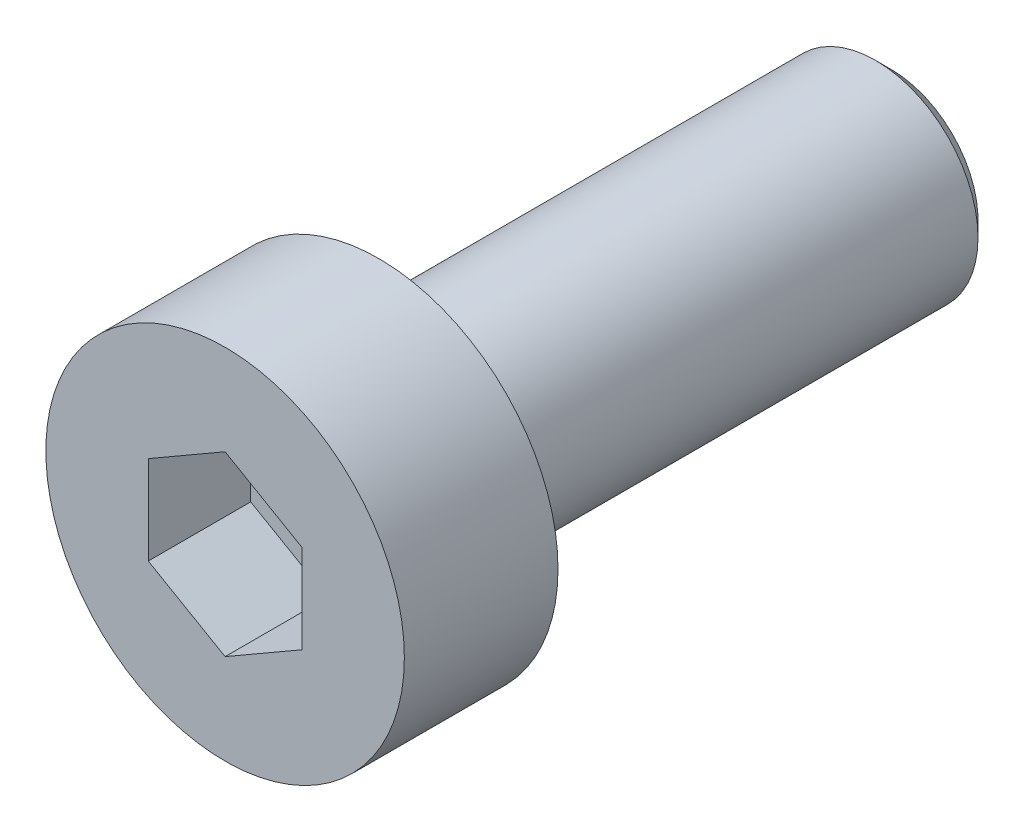
SolidWorks part; units mm, degrees
ref_plane "Front Plane" through (0, 0, 0) normal (0, 0, 1) x (1, 0, 0)
ref_plane "Top Plane" through (0, 0, 0) normal (0, 1, 0) x (1, 0, 0)
ref_plane "Right Plane" through (0, 0, 0) normal (1, 0, 0) x (0, 0, -1)
sketch "Sketch1" plane through (0, 0, 0) normal (0, 0, 1) x (1, 0, 0)
  circle A0 centre (0, 0) radius 3.5
  dimension "D1" = 7
extrude "Boss-Extrude1" add sketch "Sketch1" along normal blind 3
sketch "Sketch2" plane through (0, 0, 0) normal (0, 0, -1) x (-1, 0, 0)
  circle A0 centre (0, 0) radius 2
  dimension "D1" = 4
extrude "Boss-Extrude2" add sketch "Sketch2" along normal blind 10
chamfer "Chamfer1" distance 0.3 angle 45 1 edges at (-2, 0, -10)
sketch "Sketch3" plane through (0, 0, 3) normal (0, 0, 1) x (1, 0, 0)
  line L1 (0, 1.7321) -> (-1.5, 0.866)
  line L2 (-1.5, 0.866) -> (-1.5, -0.866)
  line L3 (-1.5, -0.866) -> (0, -1.7321)
  line L4 (0, -1.7321) -> (1.5, -0.866)
  line L5 (1.5, -0.866) -> (1.5, 0.866)
  line L6 (1.5, 0.866) -> (0, 1.7321)
  circle A0 centre (0, 0) radius 1.5 construction
  dimension "D1" = 3
extrude "Cut-Extrude1" cut sketch "Sketch3" against normal blind 2
